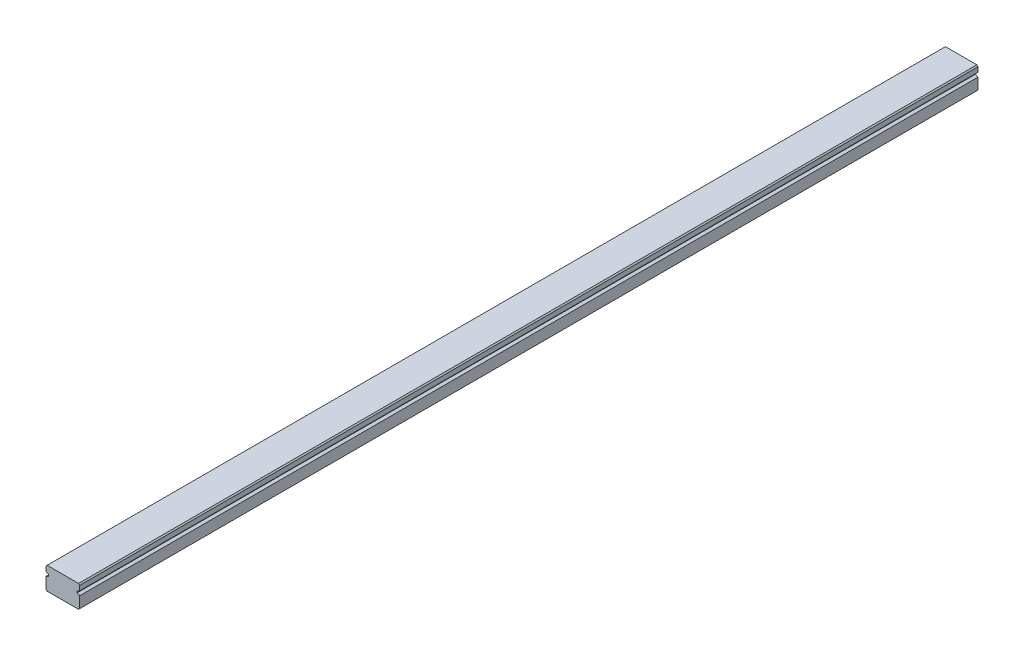
SolidWorks part; units mm, degrees
ref_plane "前视基准面" through (0, 0, 0) normal (0, 0, 1) x (1, 0, 0)
ref_plane "上视基准面" through (0, 0, 0) normal (0, 1, 0) x (1, 0, 0)
ref_plane "右视基准面" through (0, 0, 0) normal (1, 0, 0) x (0, 0, -1)
sketch "草图1" plane through (0, 0, 0) normal (0, 0, 1) x (1, 0, 0)
  line L1 (-3.269, 4.9492) -> (10.731, 4.9492)
  line L2 (-3.769, 4.4492) -> (-3.769, 2.3175)
  line L3 (-3.269, -5.0508) -> (10.731, -5.0508)
  line L4 (11.231, 4.4492) -> (11.231, 2.3175)
  line L6 (11.231, 0.4492) -> (10.0868, 0.9834)
  line L7 (10.0868, 0.9834) -> (10.0868, 1.7834)
  line L8 (-3.769, 0.4492) -> (-2.6248, 0.9834)
  line L9 (11.231, 2.3175) -> (10.0868, 1.7834)
  line L10 (-2.6248, 0.9834) -> (-2.6248, 1.7834)
  line L11 (-3.769, 2.3175) -> (-2.6248, 1.7834)
  line L12 (-3.769, 0.4492) -> (-3.769, -4.5508)
  line L13 (11.231, 0.4492) -> (11.231, -4.5508)
  line L14 (-3.769, 4.4492) -> (-3.269, 4.9492)
  line L15 (10.731, 4.9492) -> (11.231, 4.4492)
  line L16 (11.231, -4.5508) -> (10.731, -5.0508)
  line L17 (-3.769, -4.5508) -> (-3.269, -5.0508)
  point P0 (-3.769, 4.9492)
  point P1 (11.231, -5.0508)
  point P2 (-3.769, -5.0508)
  point P3 (11.231, 4.9492)
  point P15 (10.0868, 1.3834)
  dimension "D1" = 15
  dimension "D2" = 10
extrude "凸台-拉伸1" add sketch "草图1" against normal blind 400
ref_plane "基准面4" through (10.731, 4.9492, 0) normal (0, 0, 1) x (1, 0, 0)
sketch "草图3" plane through (0, 4.9492, 0) normal (0, 1, 0) x (1, 0, 0)
  line L0 (3.731, 400) -> (3.731, 0)
  line L1 (10.731, 400) -> (-3.269, 400) construction
  line L2 (10.731, 0) -> (-3.269, 0) construction
  line L3 (3.731, 200) -> (60.7851, 200)
  line L4 (24.4685, 180) -> (-12.5662, 180)
  line L5 (24.4685, 140) -> (-12.5662, 140)
  line L6 (24.4685, 100) -> (-12.5662, 100)
  line L7 (24.4685, 60) -> (-12.5662, 60)
  line L8 (24.4685, 20) -> (-12.5662, 20)
  dimension "D1" = 20
  dimension "D2" = 40
  dimension "D3" = 40
  dimension "D4" = 40
  dimension "D5" = 40
